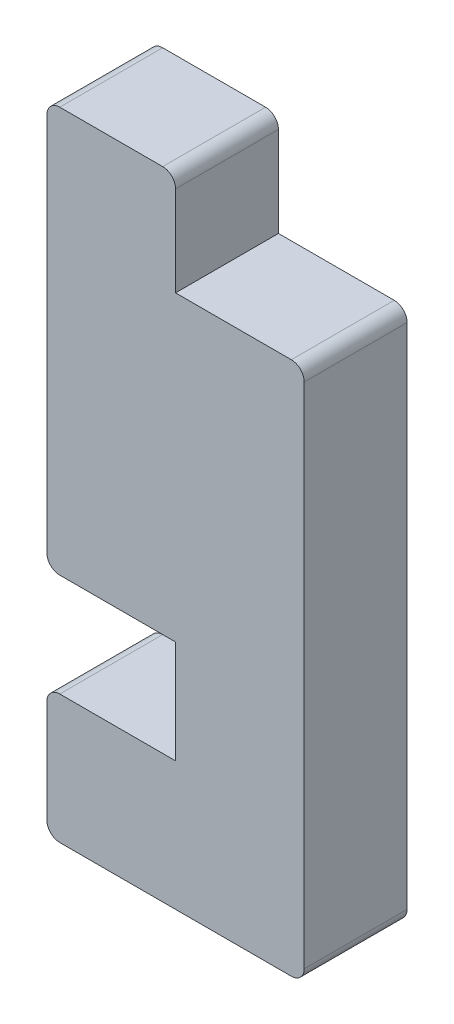
SolidWorks part; units mm, degrees
ref_plane "Front Plane" through (0, 0, 0) normal (0, 0, 1) x (1, 0, 0)
ref_plane "Top Plane" through (0, 0, 0) normal (0, 1, 0) x (1, 0, 0)
ref_plane "Right Plane" through (0, 0, 0) normal (1, 0, 0) x (0, 0, -1)
sketch "Sketch1" plane through (0, 0, 0) normal (0, 0, 1) x (1, 0, 0)
  line L0 (1, 0) -> (19, 0)
  line L1 (20, 1) -> (20, 40.5)
  line L3 (1, 49.5) -> (9, 49.5)
  line L4 (10, 48.5) -> (10, 41.5)
  line L5 (10, 41.5) -> (19, 41.5)
  line L6 (10, 10) -> (1, 10)
  line L7 (0, 9) -> (0, 1)
  line L9 (0, 48.5) -> (0, 19)
  line L10 (1, 18) -> (10, 18)
  line L11 (10, 18) -> (10, 10)
  arc A0 (1, 10) -> (0, 9) centre (1, 9) ccw
  arc A1 (0, 1) -> (1, 0) centre (1, 1) ccw
  arc A2 (19, 0) -> (20, 1) centre (19, 1) ccw
  arc A3 (1, 18) -> (0, 19) centre (1, 19) cw
  arc A4 (20, 40.5) -> (19, 41.5) centre (19, 40.5) ccw
  arc A5 (0, 48.5) -> (1, 49.5) centre (1, 48.5) cw
  arc A6 (10, 48.5) -> (9, 49.5) centre (9, 48.5) ccw
  point P16 (0, 10)
  point P19 (0, 0)
  point P22 (20, 0)
  point P25 (14.5, 41.5)
  point P29 (0, 49.5)
  point P32 (10, 49.5)
  dimension "D6" = 1
  dimension "D9" = 1
  dimension "D1" = 10
  dimension "D2" = 8
  dimension "D3" = 20
  dimension "D4" = 10
  dimension "D5" = 10
  dimension "D7" = 31.5
  dimension "D8" = 8
extrude "Boss-Extrude1" add sketch "Sketch1" along normal blind 8
